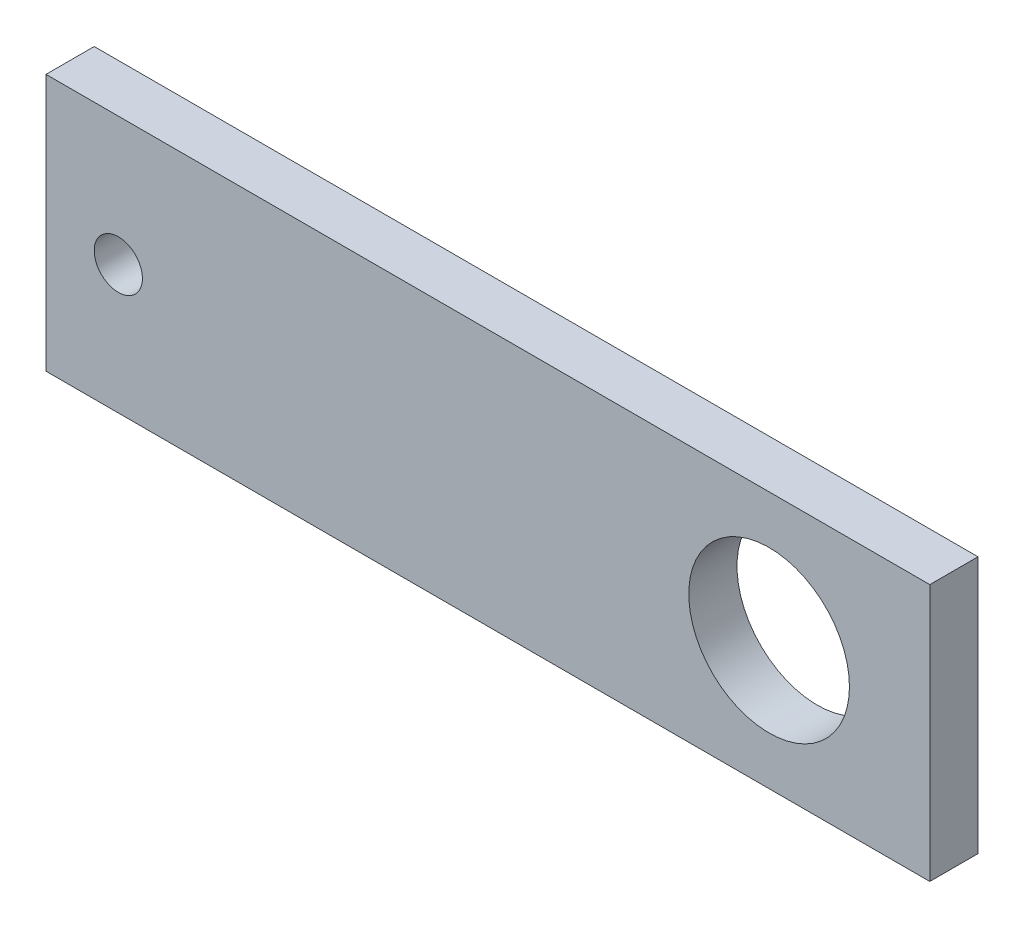
SolidWorks part; units mm, degrees
ref_plane "Plan de face" through (0, 0, 0) normal (0, 0, 1) x (1, 0, 0)
ref_plane "Plan de dessus" through (0, 0, 0) normal (0, 1, 0) x (1, 0, 0)
ref_plane "Plan de droite" through (0, 0, 0) normal (1, 0, 0) x (0, 0, -1)
sketch "Esquisse1" plane through (0, 0, 0) normal (0, 0, 1) x (1, 0, 0)
  line L1 (-45.5283, 0.7501) -> (9.4717, 0.7501)
  line L2 (-45.5283, 0.7501) -> (-45.5283, -15.2499)
  line L3 (-45.5283, -15.2499) -> (9.4717, -15.2499)
  line L4 (9.4717, 0.7501) -> (9.4717, -15.2499)
  circle A0 centre (-0.5283, -7.2499) radius 5
  circle A1 centre (-41.0283, -7.2499) radius 1.5
  dimension "D1" = 10
  dimension "D5" = 8
  dimension "D2" = 16
  dimension "D3" = 8
  dimension "D4" = 10
  dimension "D6" = 4.5
  dimension "D7" = 55
extrude "Boss.-Extru.1" add sketch "Esquisse1" along normal blind 3
